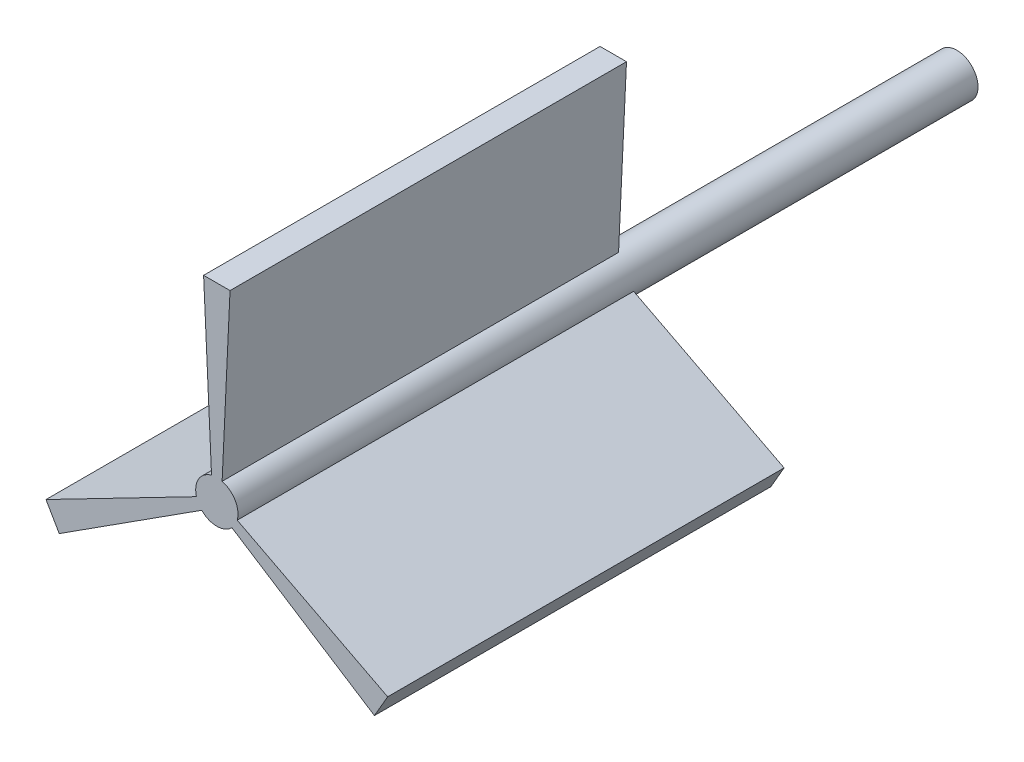
SolidWorks part; units mm, degrees
ref_plane "Front Plane" through (0, 0, 0) normal (0, 0, 1) x (1, 0, 0)
ref_plane "Top Plane" through (0, 0, 0) normal (0, 1, 0) x (1, 0, 0)
ref_plane "Right Plane" through (0, 0, 0) normal (1, 0, 0) x (0, 0, -1)
sketch "Sketch1" plane through (0, 0, 0) normal (0, 0, 1) x (1, 0, 0)
  circle A0 centre (0, 0) radius 4
  dimension "D1" = 8
extrude "Boss-Extrude1" add sketch "Sketch1" along normal blind 140
sketch "Sketch2" plane through (0, 0, 140) normal (0, 0, 1) x (1, 0, 0)
  line L0 (2.5, 35.873) -> (-2.5, 35.873)
  line L1 (-2.5, 35.873) -> (-1, 3.873)
  line L2 (2.5, 35.873) -> (1, 3.873)
  line L3 (1, 3.873) -> (-1, 3.873)
  line L4 (32.3169, -15.7714) -> (3.8541, -1.0705)
  line L5 (29.8169, -20.1016) -> (2.8541, -2.8025)
  line L6 (2.8541, -2.8025) -> (3.8541, -1.0705)
  line L7 (29.8169, -20.1016) -> (32.3169, -15.7714)
  line L8 (-29.8169, -20.1016) -> (-2.8541, -2.8025)
  line L9 (-32.3169, -15.7714) -> (-3.8541, -1.0705)
  line L10 (-3.8541, -1.0705) -> (-2.8541, -2.8025)
  line L11 (-32.3169, -15.7714) -> (-29.8169, -20.1016)
  circle A0 centre (0, 0) radius 4 construction
  point P7 (0, 35.873)
  point P19 (0, 0)
  dimension "D1" = 5
  dimension "D2" = 2
  dimension "D3" = 32
  dimension "D4" = 3
extrude "Boss-Extrude2" add sketch "Sketch2" against normal blind 75
